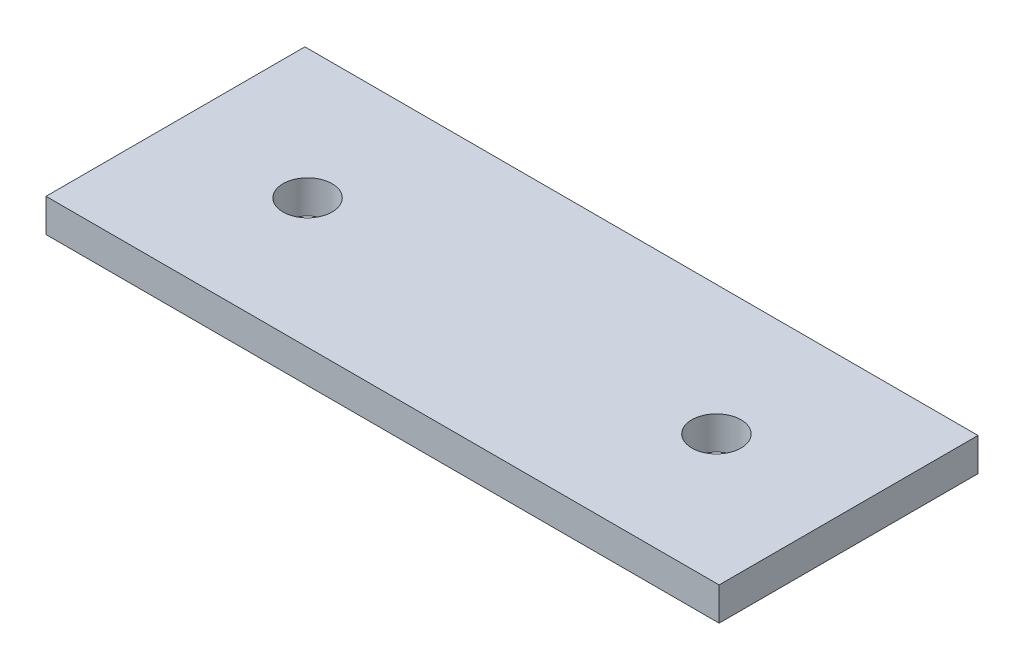
SolidWorks part; units mm, degrees
material "Acrylic (Medium-high impact)"
ref_plane "Front Plane" through (0, 0, 0) normal (0, 0, 1) x (1, 0, 0)
ref_plane "Top Plane" through (0, 0, 0) normal (0, 1, 0) x (1, 0, 0)
ref_plane "Right Plane" through (0, 0, 0) normal (1, 0, 0) x (0, 0, -1)
sketch "Sketch1" plane through (0, 0, 0) normal (0, 1, 0) x (1, 0, 0)
  line L1 (15.4781, -5.9531) -> (-15.4781, -5.9531)
  line L2 (15.4781, -5.9531) -> (15.4781, 5.9531)
  line L3 (15.4781, 5.9531) -> (-15.4781, 5.9531)
  line L4 (-15.4781, -5.9531) -> (-15.4781, 5.9531)
  line L5 (15.4781, -5.9531) -> (-15.4781, 5.9531) construction
  line L6 (15.4781, 5.9531) -> (-15.4781, -5.9531) construction
  point P0 (0, 0)
  dimension "D1" = 30.9562
  dimension "D2" = 11.9062
extrude "Boss-Extrude1" add sketch "Sketch1" along normal blind 1.524
hole_wizard "#4-40 Tapped Hole1" positions "Sketch4" profile "Sketch3" tap size "#4-40" standard "Ansi Inch"
sketch "Sketch4" plane through (0, 1.524, 0) normal (0, 1, 0) x (-1, 0, 0)
  line L0 (0, 0) -> (0, -4.4557) construction
  point P0 (9.402, 0)
  point P8 (-9.402, 0)
sketch "Sketch3" plane through (-9.402, 1.524, 0) normal (1, 0, 0) x (0, 0, 1)
  line L0 (0, 0) -> (0, 9.5692)
  line L1 (0, 9.5692) -> (1.1303, 8.89)
  line L2 (1.1303, 8.89) -> (1.1303, 0)
  line L5 (1.1303, 0) -> (0, 0)
  line L10 (0, 9.5692) -> (-1.1303, 8.89) construction
  line L11 (0, -6.35) -> (0, 107.95) construction
  dimension "Tap Drill Dia." = 2.2606
  dimension "Tap Drill Depth" = 8.89
  dimension "Drill Angle" = 118
cosmetic thread "Hole Thread1" parameters "D1"=5.588, "D2"=2.8448
cosmetic thread "Hole Thread2" parameters "D1"=5.588, "D2"=2.8448
